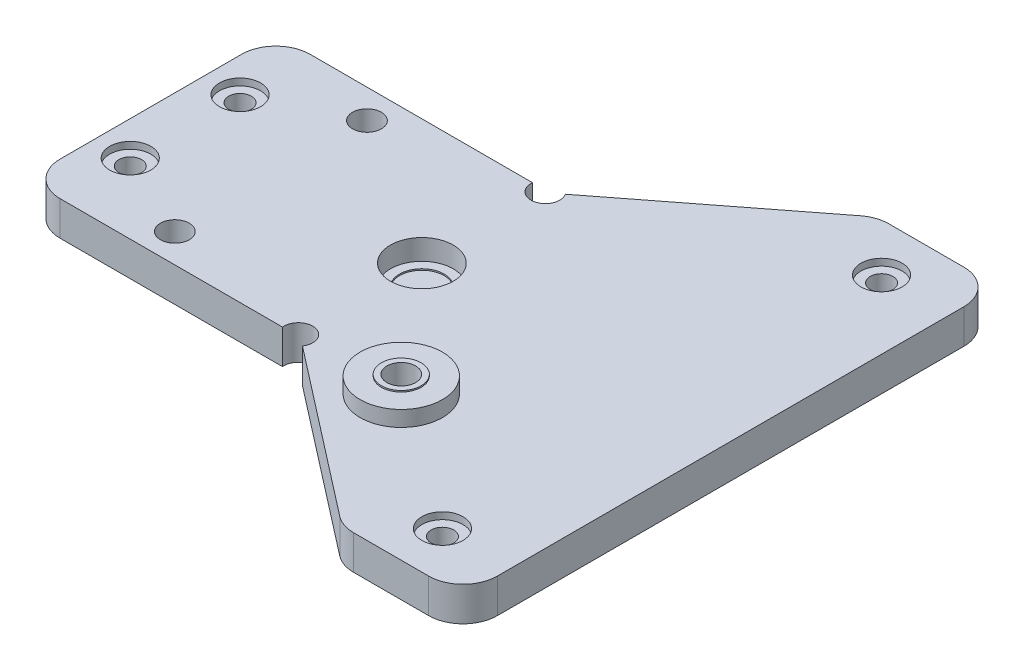
SolidWorks part; units mm, degrees
ref_plane "Front Plane" through (0, 0, 0) normal (0, 0, 1) x (1, 0, 0)
ref_plane "Top Plane" through (0, 0, 0) normal (0, 1, 0) x (1, 0, 0)
ref_plane "Right Plane" through (0, 0, 0) normal (1, 0, 0) x (0, 0, -1)
sketch "Sketch1" plane through (0, 0, 0) normal (0, 1, 0) x (1, 0, 0)
  line L0 (-22, 14) -> (-22, -14) construction
  line L1 (0, -18) -> (0, 18) construction
  line L3 (45, 30) -> (-70, 30)
  line L4 (45, 30) -> (45, -30)
  line L5 (45, -30) -> (-70, -30)
  line L6 (-70, 30) -> (-70, -30)
  circle A0 centre (-22, 14) radius 2.1
  circle A1 centre (0, 18) radius 2.1
  circle A2 centre (0, -18) radius 2.1
  circle A3 centre (-22, -14) radius 2.1
  circle A4 centre (15, -18) radius 2.1
  point P11 (-22, 0)
  point P19 (45, 0)
  dimension "D1" = 4.2
  dimension "D2" = 22
  dimension "D3" = 28
  dimension "D4" = 36
  dimension "D5" = 15
  dimension "D6" = 60
  dimension "D7" = 45
  dimension "D8" = 115
extrude "Boss-Extrude1" add sketch "Sketch1" along normal blind 5
sketch "Sketch2" plane through (0, 5, 0) normal (0, 1, 0) x (1, 0, 0)
  circle A0 centre (0, 0) radius 4.575
  dimension "D1" = 9.15
extrude "Cut-Extrude1" cut sketch "Sketch2" against normal blind 3
sketch "Sketch3" plane through (0, 2, 0) normal (0, 1, 0) x (1, 0, 0)
  circle A0 centre (0, 0) radius 3.25
  dimension "D1" = 6.5
extrude "Cut-Extrude2" cut sketch "Sketch3" against normal blind 0.2
sketch "Sketch4" plane through (0, 5, 0) normal (0, 1, 0) x (1, 0, 0)
  line L0 (-22, 18.2216) -> (-8.2975, 18.2216) construction
  line L1 (-22, -18.2216) -> (-8.2975, -18.2216) construction
  line L2 (-22, 18.2216) -> (-8.2975, 18.2216) construction
  line L3 (-22, -18.2216) -> (-8.2975, -18.2216) construction
  line L4 (-28.4216, 7.4) -> (-28.4216, 11.8) construction
  line L5 (-28.4216, -7.4) -> (-28.4216, 7.4) construction
  line L6 (-28.4216, -11.8) -> (-28.4216, -7.4) construction
  line L7 (-28.4216, 7.4) -> (-28.4216, 11.8) construction
  line L8 (-28.4216, -7.4) -> (-28.4216, 7.4) construction
  line L9 (-28.4216, -11.8) -> (-28.4216, -7.4) construction
  line L10 (-6.8288, 12.5) -> (26.8012, 38.5804) construction
  line L11 (-37.5, 12.5) -> (-6.8288, 12.5) construction
  line L14 (26.8012, -38.5804) -> (-6.8288, -12.5) construction
  line L15 (-6.8288, 12.5) -> (26.8012, 38.5804) construction
  line L16 (-37.5, 12.5) -> (-6.8288, 12.5) construction
  line L17 (-37.5, -12.5) -> (-37.5, 12.5) construction
  line L18 (-6.8288, -12.5) -> (-37.5, -12.5) construction
  line L19 (26.8012, -38.5804) -> (-6.8288, -12.5) construction
  line L20 (-34.5, 8) -> (-34.5, -8) construction
  arc A0 (-22, 18.2216) -> (-28.4216, 11.8) centre (-22, 11.8) ccw construction
  arc A1 (-28.4216, -11.8) -> (-22, -18.2216) centre (-22, -11.8) ccw construction
  arc A2 (-22, 18.2216) -> (-28.4216, 11.8) centre (-22, 11.8) ccw construction
  arc A3 (-28.4216, -11.8) -> (-22, -18.2216) centre (-22, -11.8) ccw construction
  arc A4 (-3.0173, -20.626) -> (-8.2975, -18.2216) centre (-8.2975, -25.2216) ccw construction
  arc A5 (-8.2975, 18.2216) -> (-3.0173, 20.626) centre (-8.2975, 25.2216) ccw construction
  arc A6 (-8.2975, 18.2216) -> (-3.0173, 20.626) centre (-8.2975, 25.2216) ccw construction
  arc A7 (-3.0173, -20.626) -> (-8.2975, -18.2216) centre (-8.2975, -25.2216) ccw construction
  circle A8 centre (-34.5, 8) radius 3 construction
  circle A9 centre (-34.5, -8) radius 3 construction
  circle A10 centre (-34.5, -8) radius 1.65
  circle A11 centre (-34.5, 8) radius 1.65
  point P26 (-34.5, 0)
  dimension "D1" = 6
  dimension "D2" = 3.3
  dimension "D3" = 16
  dimension "D4" = 34.5
extrude "Cut-Extrude3" cut sketch "Sketch4" against normal through all
sketch "Sketch6" plane through (0, 5, 0) normal (0, 1, 0) x (1, 0, 0)
  line L0 (-22, 18.2216) -> (-34.5, 18.2216)
  line L1 (-39.5, 13.2216) -> (-39.5, -13.2216)
  line L2 (-34.5, -18.2216) -> (-22, -18.2216)
  line L4 (-70, -30) -> (45, -30) construction
  line L5 (-22, -30) -> (-70, -30)
  line L6 (-70, -30) -> (-70, 30)
  line L7 (-70, 30) -> (-70, -30) construction
  line L8 (45, 30) -> (-70, 30) construction
  line L9 (-70, 30) -> (-22, 30)
  line L11 (-34.5, 8) -> (-34.5, -8) construction
  line L12 (-22, -18.2216) -> (-8.2975, -18.2216) construction
  line L13 (-22, 18.2216) -> (-8.2975, 18.2216) construction
  line L14 (-22, 18.2216) -> (-8.2975, 18.2216)
  line L15 (-22, -18.2216) -> (-8.2975, -18.2216)
  line L22 (26.8012, 38.5804) -> (-22, 30)
  line L23 (26.8012, -38.5804) -> (-22, -30)
  line L25 (-8.2975, 18.2216) -> (0.549, 18.2216)
  line L26 (-6.8288, 12.5) -> (26.8012, 38.5804) construction
  line L27 (0.549, 18.2216) -> (26.8012, 38.5804)
  line L28 (-8.2975, -18.2216) -> (0.549, -18.2216)
  line L29 (0.549, -18.2216) -> (26.8012, -38.5804)
  line L30 (26.8012, -38.5804) -> (-6.8288, -12.5) construction
  arc A0 (-34.5, 18.2216) -> (-39.5, 13.2216) centre (-34.5, 13.2216) ccw
  arc A1 (-39.5, -13.2216) -> (-34.5, -18.2216) centre (-34.5, -13.2216) ccw
  point P2 (-3.0167, -18.2216)
  point P23 (15.8424, -35.8981)
  point P31 (19.3012, 38.5804)
  point P33 (19.3012, -38.5804)
  dimension "D2" = 5
  dimension "D1" = 5
extrude "Cut-Extrude4" cut sketch "Sketch6" against normal through all
sketch "Sketch7" plane through (0, 5, 0) normal (0, 1, 0) x (1, 0, 0)
  line L0 (27.3422, 39) -> (15.7369, 30)
  line L1 (15.7369, 30) -> (45, 30)
  line L2 (45, 30) -> (45, 39)
  line L3 (45, -30) -> (15.7369, -30)
  line L4 (15.7369, -30) -> (27.3422, -39)
  line L5 (27.3422, -39) -> (45, -39)
  line L6 (45, -39) -> (45, -30)
  line L7 (45, 39) -> (27.3422, 39)
  line L10 (-6.8288, 12.5) -> (26.8012, 38.5804) construction
  line L11 (45, 30) -> (15.7369, 30) construction
  line L12 (26.8012, -38.5804) -> (-6.8288, -12.5) construction
  line L13 (15.7369, -30) -> (45, -30) construction
  point P2 (26.8012, 38.5804)
  point P4 (15.7369, 30)
  point P18 (15.7369, -30)
  point P24 (26.8012, -39.4196)
  point P25 (26.8012, -38.5804)
  point P27 (26.8012, -41.2176)
  point P28 (30.7714, 39.7977)
  point P29 (30.2633, -46.0814)
  dimension "D1" = 78
extrude "Boss-Extrude2" add sketch "Sketch7" against normal up to surface (5 mm away) up to face at (-2.3283, 0, 0)
sketch "Sketch8" plane through (0, 5, 0) normal (0, 1, 0) x (1, 0, 0)
  line L0 (35, 32) -> (35, -32) construction
  circle A0 centre (35, 32) radius 1.65
  circle A1 centre (35, -32) radius 1.65
  circle A2 centre (35, 32) radius 3 construction
  circle A3 centre (35, -32) radius 3 construction
  point P6 (35, 0)
  dimension "D1" = 6
  dimension "D2" = 3.3
  dimension "D3" = 35
  dimension "D4" = 64
extrude "Cut-Extrude5" cut sketch "Sketch8" against normal through all
fillet "Fillet1" radius 5 4 edges at (45, 2.5, 39) (27.3422, 2.5, 39) (27.3422, 2.5, -39) (45, 2.5, -39)
sketch "Sketch9" plane through (0, 5, 0) normal (0, 1, 0) x (1, 0, 0)
  circle A0 centre (15, -18) radius 6
  circle A1 centre (15, -18) radius 2.1 construction
  circle A2 centre (15, -18) radius 2.1
  dimension "D1" = 12
extrude "Boss-Extrude3" add sketch "Sketch9" along normal blind 2.275
sketch "Sketch10" plane through (0, 7.275, 0) normal (0, 1, 0) x (1, 0, 0)
  circle A0 centre (15, -18) radius 2.9
  circle A1 centre (15, -18) radius 2.1 construction
  circle A2 centre (15, -18) radius 2.1
  dimension "D1" = 0.8
extrude "Boss-Extrude4" add sketch "Sketch10" along normal blind 0.2
sketch "Sketch11" plane through (0, 5, 0) normal (0, 1, 0) x (1, 0, 0)
  circle A0 centre (-34.5, 8) radius 3
  circle A1 centre (-34.5, -8) radius 3
  circle A2 centre (35, -32) radius 3
  circle A3 centre (35, 32) radius 3
  dimension "D1" = 6
extrude "Cut-Extrude6" cut sketch "Sketch11" against normal blind 1
